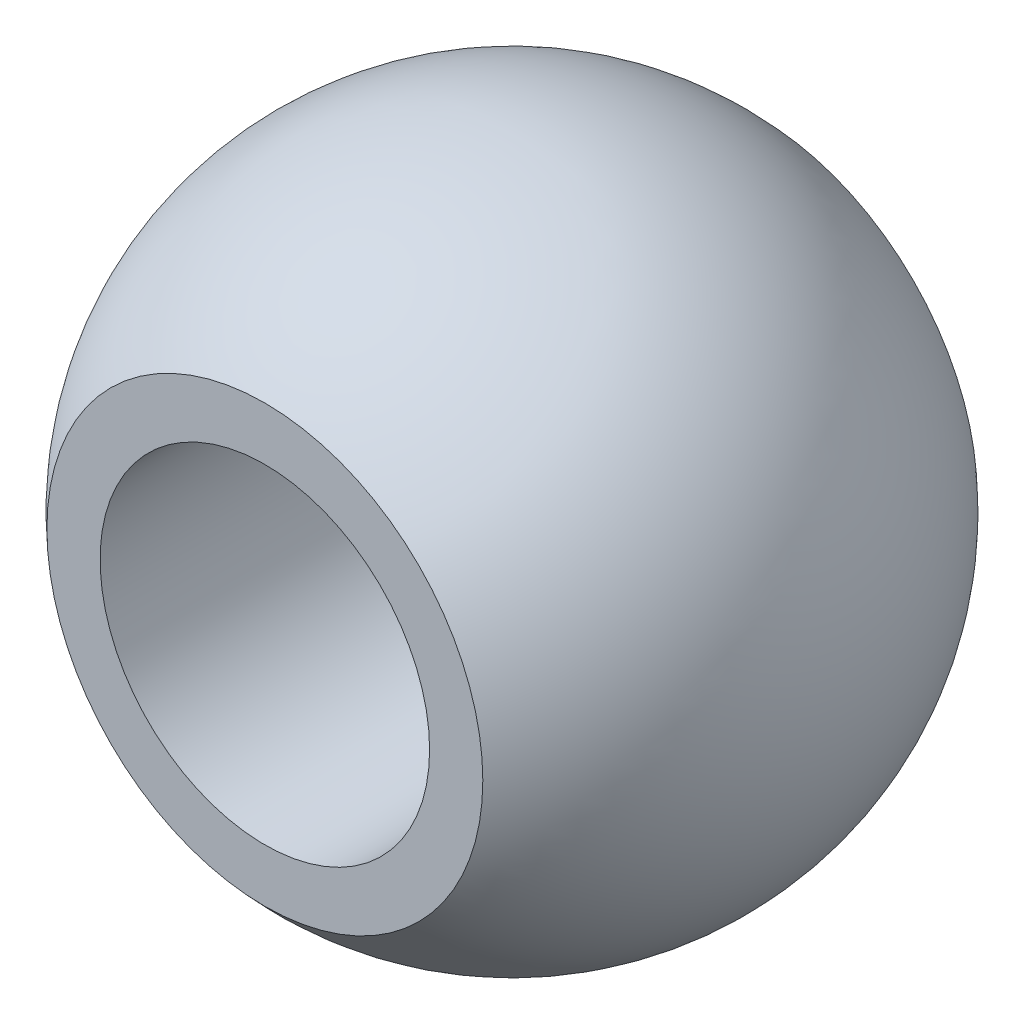
SolidWorks part; units mm, degrees
material "Alloy Steel"
ref_plane "Front Plane" through (0, 0, 0) normal (0, 0, 1) x (1, 0, 0)
ref_plane "Top Plane" through (0, 0, 0) normal (0, 1, 0) x (1, 0, 0)
ref_plane "Right Plane" through (0, 0, 0) normal (1, 0, 0) x (0, 0, -1)
sketch "Sketch1" plane through (0, 0, 0) normal (0, 1, 0) x (1, 0, 0)
  line L0 (0, 5.8396) -> (0, -6) construction
  line L1 (-5.2915, 6) -> (0, 6)
  line L2 (-5.2915, -6) -> (0, -6)
  line L3 (0, 6) -> (0, -6)
  line L4 (0, -8) -> (0, -8.2851) construction
  arc A0 (-5.2915, 6) -> (-5.2915, -6) centre (0, 0) ccw
  dimension "D1" = 16
  dimension "D2" = 12
  dimension "D3" = 6
revolve "Revolve1" add sketch "Sketch1" angle 360 about L3
sketch "Sketch2" plane through (0, 0, 6) normal (0, 0, 1) x (1, 0, 0)
  circle A0 centre (0, 0) radius 4
  dimension "D1" = 8
extrude "Cut-Extrude1" cut sketch "Sketch2" against normal blind 17
